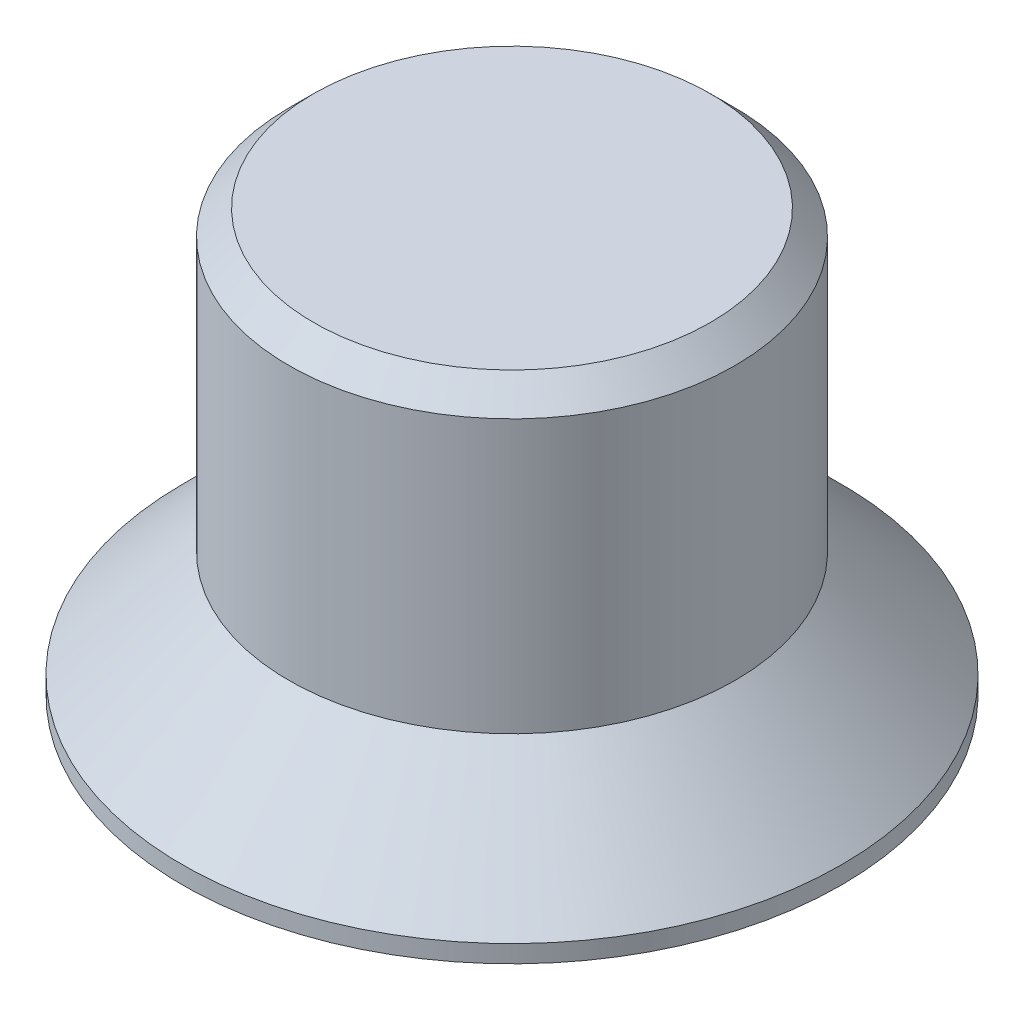
SolidWorks part; units mm, degrees
ref_plane "Front Plane" through (0, 0, 0) normal (0, 0, 1) x (1, 0, 0)
ref_plane "Top Plane" through (0, 0, 0) normal (0, 1, 0) x (1, 0, 0)
ref_plane "Right Plane" through (0, 0, 0) normal (1, 0, 0) x (0, 0, -1)
sketch "Sketch1" plane through (0, 0, 0) normal (0, 0, 1) x (1, 0, 0)
  line L0 (0, 0.25) -> (1.5, 0.25)
  line L1 (1.5, 0.25) -> (1.5441, 0)
  line L2 (1.5441, 0) -> (3.5, 0)
  line L3 (3.5, 0) -> (2.25, 1.25)
  line L4 (2.25, 1.25) -> (2.25, 4.25)
  line L5 (2.25, 4.25) -> (0, 4.25)
  line L6 (0, 4.25) -> (0, 0.25)
  line L7 (0, -277.7981) -> (0, 13612.105) construction
  dimension "D1" = 1.5
  dimension "D2" = 100
  dimension "D3" = 45
  dimension "D4" = 2.25
  dimension "D5" = 0.25
  dimension "D6" = 3
  dimension "D7" = 3.5
revolve "Revolve1" add sketch "Sketch1" angle 360 about L7
chamfer "Chamfer1" distance 0.25 angle 45 1 edges at (2.25, 4.25, 0)
chamfer "Chamfer2" distance 0.25 angle 45 1 edges at (3.5, 0, 0)
